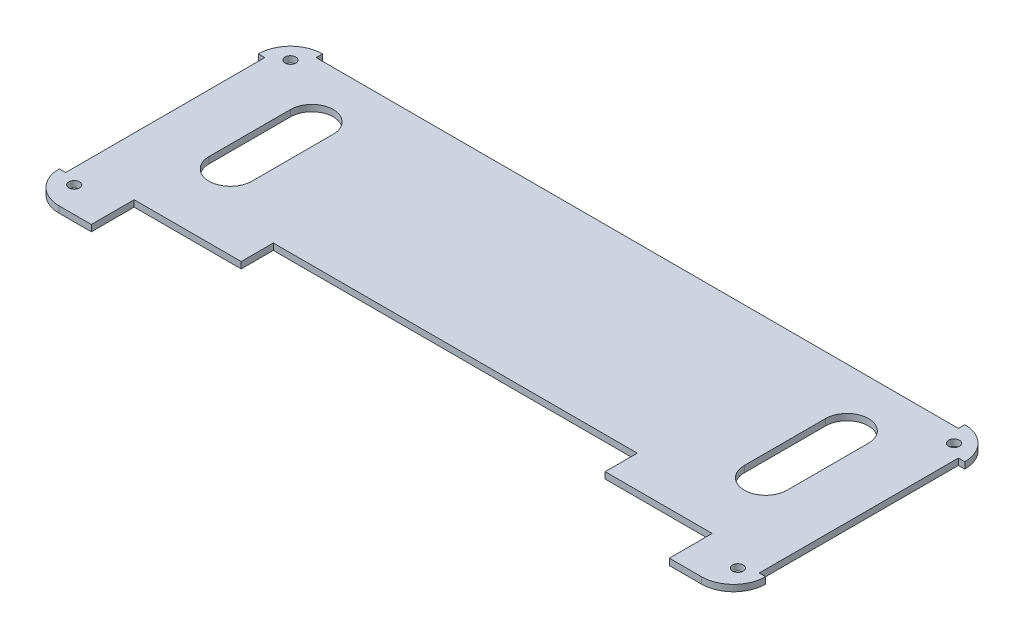
SolidWorks part; units mm, degrees
ref_plane "Plan de face" through (0, 0, 0) normal (0, 0, 1) x (1, 0, 0)
ref_plane "Plan de dessus" through (0, 0, 0) normal (0, 1, 0) x (1, 0, 0)
ref_plane "Plan de droite" through (0, 0, 0) normal (1, 0, 0) x (0, 0, -1)
sketch "Esquisse1" plane through (0, 0, 0) normal (0, 1, 0) x (1, 0, 0)
  line L0 (0, 113) -> (330, 113) construction
  line L1 (0, 0) -> (30, 0)
  line L2 (0, 0) -> (0, 123)
  line L3 (0, 123) -> (330, 123)
  line L4 (330, 0) -> (330, 123)
  line L5 (30, 93) -> (50, 93) construction
  line L6 (165, 123) -> (165, 0) construction
  line L7 (10, 123) -> (10, 0) construction
  line L8 (30, 0) -> (30, 20)
  line L9 (30, 20) -> (80, 20)
  line L10 (0, 0) -> (330, 0) construction
  line L11 (300, 0) -> (300, 20)
  line L12 (330, 0) -> (300, 0)
  line L13 (300, 93) -> (300, 55)
  line L14 (280, 93) -> (280, 55)
  line L15 (30, 93) -> (30, 55)
  line L17 (50, 93) -> (50, 55)
  line L21 (80, 20) -> (80, 35)
  line L22 (80, 35) -> (250, 35)
  line L23 (250, 20) -> (250, 35)
  line L24 (300, 20) -> (250, 20)
  circle A0 centre (10, 113) radius 2.5
  circle A1 centre (320, 113) radius 2.5
  circle A2 centre (10, 12) radius 2.5
  circle A3 centre (320, 12) radius 2.5
  arc A4 (30, 93) -> (50, 93) centre (40, 93) cw
  arc A5 (30, 55) -> (50, 55) centre (40, 55) ccw
  arc A6 (300, 93) -> (280, 93) centre (290, 93) ccw
  arc A7 (300, 55) -> (280, 55) centre (290, 55) cw
  point P13 (10, 113)
  point P26 (165, 35)
  point P39 (165, 35)
  dimension "D3" = 5
  dimension "D12" = 5
  dimension "D1" = 330
  dimension "D2" = 123
  dimension "D4" = 10
  dimension "D5" = 10
  dimension "D6" = 20
  dimension "D7" = 20
  dimension "D8" = 20
  dimension "D9" = 30
  dimension "D10" = 30
  dimension "D11" = 55
  dimension "D13" = 12
  dimension "D14" = 50
  dimension "D15" = 35
extrude "Extrusion1" add sketch "Esquisse1" along normal blind 3
fillet "Congé1" radius 15 4 edges at (0, 1.5, 0) (330, 1.5, 0) (330, 1.5, -123) (0, 1.5, -123)
sketch "Esquisse2" plane through (0, 3, 0) normal (0, 1, 0) x (1, 0, 0)
  line L0 (0, 108) -> (3, 108)
  line L1 (3, 108) -> (3, 15)
  line L2 (3, 15) -> (0, 15)
  line L3 (0, 15) -> (0, 108)
  line L4 (15, 123) -> (15, 120)
  line L5 (165, 123) -> (165, 35) construction
  line L6 (315, 123) -> (15, 123) construction
  line L7 (80, 35) -> (250, 35) construction
  line L8 (15, 120) -> (315, 120)
  line L9 (15, 123) -> (315, 123)
  line L10 (330, 15) -> (330, 108)
  line L11 (327, 15) -> (330, 15)
  line L12 (327, 108) -> (327, 15)
  line L13 (330, 108) -> (327, 108)
  line L14 (315, 123) -> (315, 120)
  point P22 (165, 120)
  dimension "D1" = 3
  dimension "D2" = 3
extrude "Extrusion2" cut sketch "Esquisse2" against normal up to next
